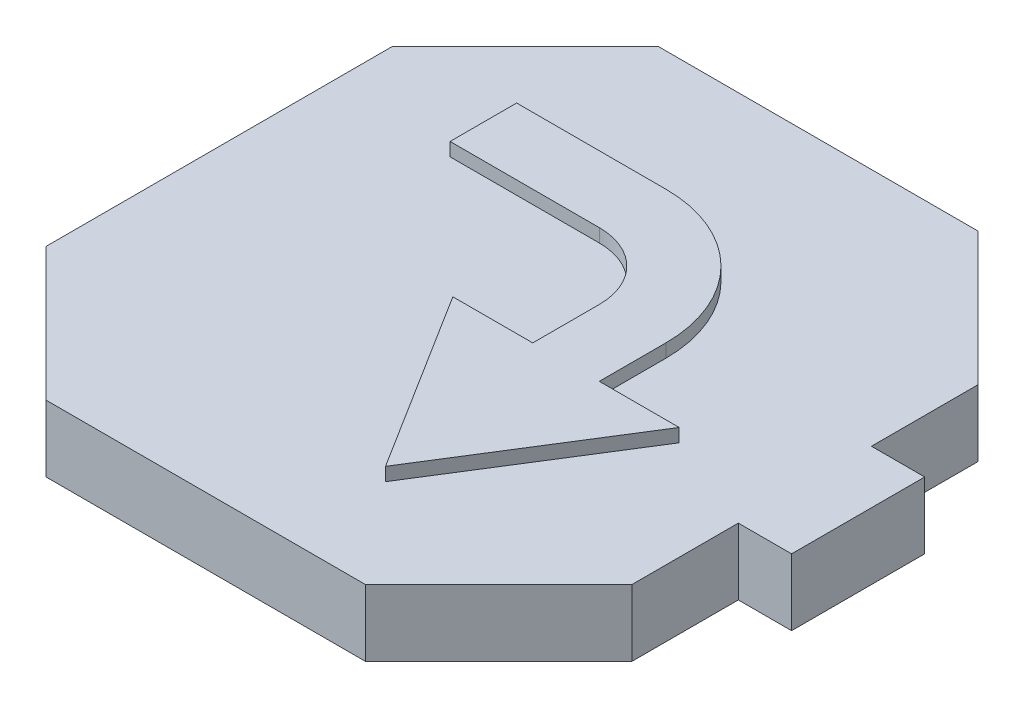
SolidWorks part; units mm, degrees
ref_plane "Plan de face" through (0, 0, 0) normal (0, 0, 1) x (1, 0, 0)
ref_plane "Plan de dessus" through (0, 0, 0) normal (0, 1, 0) x (1, 0, 0)
ref_plane "Plan de droite" through (0, 0, 0) normal (1, 0, 0) x (0, 0, -1)
sketch "Esquisse1" plane through (0, 0, 0) normal (0, 1, 0) x (1, 0, 0)
  line L0 (22, 13) -> (12.003, 23)
  line L1 (22, 13) -> (22, 5)
  line L2 (-22, -13) -> (-22, 13)
  line L3 (22, 5) -> (26, 5)
  line L4 (22, -5) -> (22, -13)
  line L5 (-22, -13) -> (22, 13) construction
  line L6 (-22, 13) -> (22, -13) construction
  line L7 (12.003, 23) -> (-12.003, 23)
  line L8 (-12.003, 23) -> (-22, 13)
  line L9 (-22, -13) -> (-12.003, -23)
  line L10 (-12.003, -23) -> (12.003, -23)
  line L11 (12.003, -23) -> (22, -13)
  line L12 (0, 23) -> (0, 0) construction
  line L13 (0, 0) -> (0, -23) construction
  line L14 (22, -5) -> (26, -5)
  line L15 (26, 5) -> (26, -5)
  point P1 (0, 0)
  dimension "D1" = 26
  dimension "D2" = 44
  dimension "D3" = 23
  dimension "D4" = 23
  dimension "D5" = 14.14
  dimension "D6" = 14.14
  dimension "D7" = 14.14
  dimension "D8" = 14.14
  dimension "D9" = 8
  dimension "D10" = 8
  dimension "D11" = 4
extrude "Boss.-Extru.1" add sketch "Esquisse1" along normal blind 5
sketch "Esquisse2" plane through (0, 5, 0) normal (0, 1, 0) x (1, 0, 0)
  line L0 (-12.652, 13) -> (-12.652, 8)
  line L1 (-12.652, 8) -> (3.5561, 8)
  line L2 (3.5561, 8) -> (3.5561, -2)
  line L3 (-2.4439, -2) -> (6.0561, -15.5554)
  line L4 (6.0561, -15.5554) -> (14.5561, -2)
  line L5 (14.5561, -2) -> (8.5561, -2)
  line L6 (8.5561, -2) -> (8.5561, 13)
  line L7 (8.5561, 13) -> (-12.652, 13)
  line L8 (3.5561, -2) -> (-2.4439, -2)
  line L9 (-22, 13) -> (-22, -13) construction
  line L10 (12.003, 23) -> (-12.003, 23) construction
  line L11 (22, 5) -> (22, 13) construction
  line L12 (8.5561, -2) -> (3.5561, -2) construction
  line L13 (6.0561, -15.5554) -> (6.0561, -2) construction
  dimension "D1" = 5
  dimension "D2" = 5
  dimension "D3" = 6
  dimension "D4" = 6
  dimension "D5" = 10
  dimension "D6" = 15
  dimension "D7" = 16
extrude "Boss.-Extru.2" add sketch "Esquisse2" along normal blind 1
sketch "Esquisse3" plane through (0, 0, 0) normal (0, -1, 0) x (1, 0, 0)
  line L0 (-12.003, 23) -> (12.003, 23) construction
  line L1 (-16, 17) -> (-10.8, 17)
  line L2 (-16, 17) -> (-16, 11.8)
  line L3 (-16, 11.8) -> (-10.8, 11.8)
  line L4 (-10.8, 17) -> (-10.8, 11.8)
  line L5 (-16, 17) -> (-10.8, 11.8) construction
  line L6 (-16, 11.8) -> (-10.8, 17) construction
  line L8 (-22, -13) -> (-22, 13) construction
  line L9 (12.003, -23) -> (-12.003, -23) construction
  line L10 (-16, -17) -> (-10.8, -17)
  line L11 (-16, -17) -> (-16, -11.8)
  line L12 (-16, -11.8) -> (-10.8, -11.8)
  line L13 (-10.8, -17) -> (-10.8, -11.8)
  line L14 (-16, -17) -> (-10.8, -11.8) construction
  line L15 (-16, -11.8) -> (-10.8, -17) construction
  line L16 (11.8, -11.8) -> (17, -11.8)
  line L17 (11.8, -11.8) -> (11.8, -17)
  line L18 (11.8, -17) -> (17, -17)
  line L19 (17, -11.8) -> (17, -17)
  line L20 (11.8, -11.8) -> (17, -17) construction
  line L21 (11.8, -17) -> (17, -11.8) construction
  line L22 (10.8, 11.8) -> (16, 11.8)
  line L23 (10.8, 11.8) -> (10.8, 17)
  line L24 (10.8, 17) -> (16, 17)
  line L25 (16, 11.8) -> (16, 17)
  line L26 (10.8, 11.8) -> (16, 17) construction
  line L27 (10.8, 17) -> (16, 11.8) construction
  line L28 (22, -5) -> (22, -13) construction
  line L29 (22, 13) -> (22, 5) construction
  line L31 (-2.5, -2.5) -> (2.5, -2.5)
  line L32 (-2.5, -2.5) -> (-2.5, 2.5)
  line L33 (-2.5, 2.5) -> (2.5, 2.5)
  line L34 (2.5, -2.5) -> (2.5, 2.5)
  line L35 (-2.5, -2.5) -> (2.5, 2.5) construction
  line L36 (-2.5, 2.5) -> (2.5, -2.5) construction
  point P0 (-13.4, 14.4)
  point P9 (-13.4, -14.4)
  point P14 (14.4, -14.4)
  point P19 (13.4, 14.4)
  point P30 (0, 0)
  dimension "D1" = 5.2
  dimension "D2" = 5.2
  dimension "D3" = 6
  dimension "D4" = 6
  dimension "D5" = 5.2
  dimension "D6" = 5.2
  dimension "D7" = 5.2
  dimension "D8" = 5.2
  dimension "D9" = 5.2
  dimension "D10" = 5.2
  dimension "D11" = 6
  dimension "D12" = 6
  dimension "D13" = 6
  dimension "D14" = 5
  dimension "D15" = 6
  dimension "D16" = 6
  dimension "D17" = 5
  dimension "D18" = 5
  dimension "D19" = 20.5
  dimension "D20" = 20.5
  dimension "D21" = 19.5
  dimension "D22" = 19.5
extrude "Enlèv. mat.-Extru.1" cut sketch "Esquisse3" against normal blind 4.8
fillet "Congé1" radius 10 1 edges at (8.5561, 5.5, -13)
fillet "Congé2" radius 5 1 edges at (3.5561, 5.5, -8)
